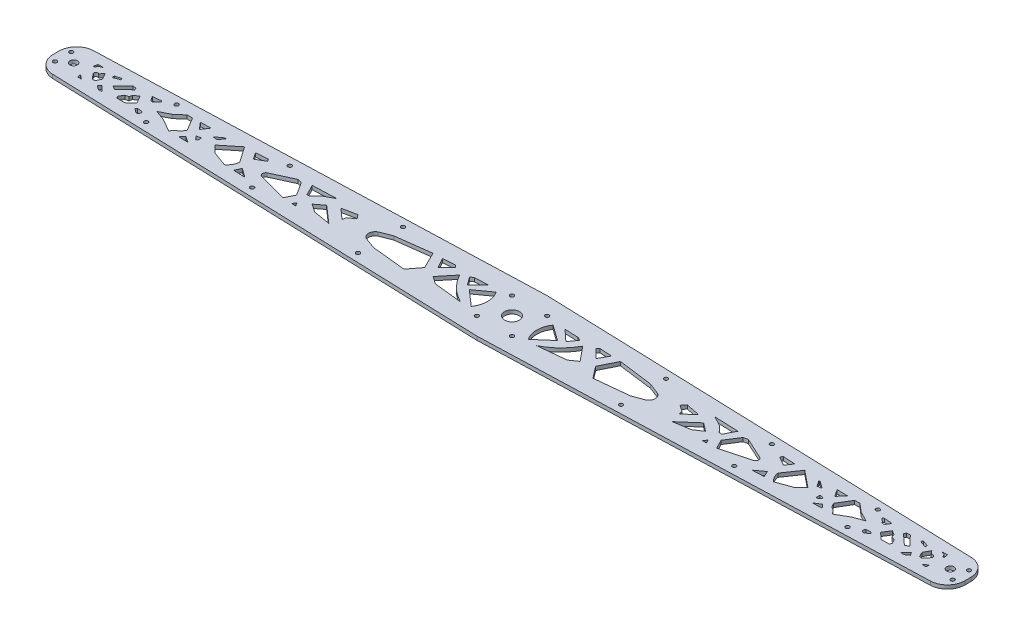
SolidWorks part; units mm, degrees
material "6061-T6 (SS)"
ref_plane "Front Plane" through (0, 0, 0) normal (0, 0, 1) x (1, 0, 0)
ref_plane "Top Plane" through (0, 0, 0) normal (0, 1, 0) x (1, 0, 0)
ref_plane "Right Plane" through (0, 0, 0) normal (1, 0, 0) x (0, 0, -1)
sketch "Sketch2" plane through (0, 0, 0) normal (0, 1, 0) x (1, 0, 0)
  line L0 (0, 0) -> (0, 30) construction
  line L1 (0, 0) -> (0, -30) construction
  line L2 (0, 0) -> (-375, 0) construction
  line L3 (-375, 17.5) -> (0, 30)
  line L4 (-375, -17.5) -> (0, -30)
  line L5 (375, -17.5) -> (0, -30)
  line L6 (375, 17.5) -> (0, 30)
  line L7 (-375, 17.5) -> (-375.4997, 17.4833)
  line L8 (-390, 2.4917) -> (-390, -2.4917)
  line L9 (-375.4997, -17.4833) -> (-375, -17.5)
  line L10 (-375, 17.5) -> (-375, -17.5) construction
  line L11 (390, 2.4917) -> (390, -2.4917)
  line L12 (375.4997, -17.4833) -> (375, -17.5)
  line L13 (375, 17.5) -> (375, -17.5) construction
  line L14 (375, 17.5) -> (375.4997, 17.4833)
  arc A2 (390, -2.4917) -> (375.4997, -17.4833) centre (375, -2.4917) cw
  arc A3 (390, 2.4917) -> (375.4997, 17.4833) centre (375, 2.4917) ccw
  arc A4 (-390, -2.4917) -> (-375.4997, -17.4833) centre (-375, -2.4917) ccw
  arc A5 (-375.4997, 17.4833) -> (-390, 2.4917) centre (-375, 2.4917) ccw
  point P15 (390, -17)
  point P18 (390, 17)
  point P21 (-390, -17)
  point P24 (-390, 17)
  point P26 (-390, 0)
  point P27 (390, 0)
  point P28 (375, 0)
  dimension "D4" = 15
  dimension "D1" = 60
  dimension "Half of Chassis Width" = 375
  dimension "FullLength" = 390
  dimension "D2" = 35
extrude "Boss-Extrude1" add sketch "Sketch2" along normal blind 3.18
sketch "Sketch3" plane through (0, 3.18, 0) normal (0, 1, 0) x (1, 0, 0)
  line L0 (0, 30) -> (0, -30) construction
  line L1 (-375, 0) -> (0, 0) construction
  line L2 (-390, 0) -> (-375, 0) construction
  line L3 (-206.25, 16.125) -> (-206.25, 0) construction
  line L4 (-112.5, -19.25) -> (-112.5, 0) construction
  line L5 (-390, 2.4917) -> (-390, -2.4917) construction
  line L6 (-375.4997, -17.4833) -> (0, -30) construction
  line L7 (-206.25, 16.125) -> (-206.25, 23.125) construction
  line L8 (0, 30) -> (-375.4997, 17.4833) construction
  line L9 (-112.5, -19.25) -> (-112.5, -26.25) construction
  line L10 (-375, 0) -> (-375, 17.5) construction
  line L11 (0, 30) -> (-375.4997, 17.4833) construction
  line L12 (-15, 0) -> (-15, 29.5) construction
  line L13 (-15, 15) -> (0, 15) construction
  line L14 (-300, 13) -> (-300, 0) construction
  line L15 (-300, 13) -> (-300, 20) construction
  circle A0 centre (0, 0) radius 6.35
  circle A1 centre (-375, 0) radius 3.175
  circle A3 centre (-206.25, 16.125) radius 1.65
  circle A4 centre (-112.5, -19.25) radius 1.65
  circle A8 centre (375, 0) radius 3.175
  circle A9 centre (-112.5, 19.25) radius 1.65
  circle A10 centre (-206.25, -16.125) radius 1.65
  circle A11 centre (112.5, -19.25) radius 1.65
  circle A12 centre (112.5, 19.25) radius 1.65
  circle A13 centre (206.25, -16.125) radius 1.65
  circle A14 centre (206.25, 16.125) radius 1.65
  circle A15 centre (-384, 7) radius 1.65
  circle A16 centre (-384, -7) radius 1.65
  circle A17 centre (384, -7) radius 1.65
  circle A18 centre (384, 7) radius 1.65
  circle A19 centre (-15, 15) radius 1.65
  circle A20 centre (-15, -15) radius 1.65
  circle A21 centre (15, -15) radius 1.65
  circle A22 centre (15, 15) radius 1.65
  circle A23 centre (-300, 13) radius 1.65
  circle A25 centre (-300, -13) radius 1.65
  circle A26 centre (300, -13) radius 1.65
  circle A27 centre (300, 13) radius 1.65
  dimension "D1" = 12.7
  dimension "D2" = 6.35
  dimension "D3" = 3.3
  dimension "Hole2" = 206.25
  dimension "Hole1" = 112.5
  dimension "D5" = 7
  dimension "D6" = 7
  dimension "BallJointHoles" = 375
  dimension "D4" = 9
  dimension "D7" = 7
  dimension "D8" = 15
  dimension "D9" = 15
  dimension "D10" = 7
  dimension "Hole3" = 300
extrude "Cut-Extrude1" cut sketch "Sketch3" against normal through all
sketch "Sketch7" plane through (0, 3.18, 0) normal (0, 1, 0) x (1, 0, 0)
  line L0 (-24.4071, -10.4422) -> (-37.738, 1.1764)
  line L1 (-37.738, 1.1764) -> (-24.4071, 10.7567)
  line L2 (-47.0329, 10.7567) -> (-42.1001, 3.9894)
  line L3 (-42.1001, 3.9894) -> (-32.5606, 12.795)
  line L5 (-62.9011, -4.6207) -> (-52.6865, 7.8247)
  line L6 (-32.5606, -11.6065) -> (-56.4435, -9.0822)
  line L7 (-56.4435, -9.0822) -> (-62.9011, -4.6207)
  line L8 (-67.5882, 4.294) -> (-60.2096, 11.6727)
  line L9 (-60.2096, 11.6727) -> (-61.9766, 13.4397)
  line L10 (-61.9766, 13.4397) -> (-72.2685, 12.795)
  line L11 (-72.2685, 12.795) -> (-67.5882, 4.294)
  line L12 (-47.0329, 10.7567) -> (-44.3117, 12.2755)
  line L13 (-44.3117, 12.2755) -> (-32.5606, 12.795)
  line L14 (-80.1851, 12.5584) -> (-73.1499, -1.5885)
  line L15 (-73.1499, -1.5885) -> (-80.8351, -11.6065)
  line L16 (-80.8351, -11.6065) -> (-109.8171, -8.6237)
  line L17 (-109.8171, -8.6237) -> (-119.4522, -5.1061)
  line L18 (-80.1851, 12.5584) -> (-109.8171, 8.7349)
  line L19 (-109.8171, 8.7349) -> (-119.4522, 4.9496)
  line L20 (-152.9555, 6.5926) -> (-140.8601, 9.0803)
  line L21 (-140.8601, 9.0803) -> (-138.158, 5.6061)
  line L22 (-138.158, 5.6061) -> (-143.5194, 1.9603)
  line L23 (-143.5194, 1.9603) -> (-144.1313, -1.2523)
  line L24 (-144.1313, -1.2523) -> (-152.9555, 6.5926)
  line L25 (-161.2336, 2.6701) -> (-146.9078, -9.8349)
  line L26 (-146.9078, -9.8349) -> (-161.2336, -7.5187)
  line L27 (-161.2336, -7.5187) -> (-168.3536, -2.7149)
  line L28 (-168.3536, -2.7149) -> (-161.2336, 2.6701)
  line L29 (-177.4895, -11.0358) -> (-174.0153, -11.0358)
  line L30 (-174.0153, -11.0358) -> (-175.7524, -8.1621)
  line L31 (-175.7524, -8.1621) -> (-177.4895, -11.0358)
  line L32 (-161.7297, 11.9502) -> (-182.144, 11.1941)
  line L33 (-182.144, 11.1941) -> (-177.4895, 2.1211)
  line L34 (-177.4895, 2.1211) -> (-175.1124, 2.1211)
  line L35 (-175.1124, 2.1211) -> (-170.3995, 7.2877)
  line L36 (-170.3995, 7.2877) -> (-161.7297, 11.9502)
  line L37 (-185.5062, -10.4422) -> (-181.6336, -2.7149)
  line L38 (-181.6336, -2.7149) -> (-188.9486, 8.7349)
  line L39 (-188.9486, 8.7349) -> (-192.6595, 9.5525)
  line L40 (-192.6595, 9.5525) -> (-210.8078, 1.1764)
  line L41 (-185.5062, -10.4422) -> (-210.0763, -3.869)
  line L45 (-224.6603, -6.0416) -> (-216.9788, -11.6065)
  line L46 (-216.9788, -11.6065) -> (-226.8789, -11.1945)
  line L47 (-226.8789, -11.1945) -> (-224.6603, -6.0416)
  line L48 (-230.6562, 11.1941) -> (-226.7322, 5.473)
  line L49 (-226.7322, 5.473) -> (-219.0389, 9.9382)
  line L50 (-219.0389, 9.9382) -> (-220.3165, 11.8009)
  line L51 (-220.3165, 11.8009) -> (-230.6562, 11.1941)
  line L52 (-234.9681, -11.0358) -> (-247.8251, -6.3663)
  line L53 (-247.8251, -6.3663) -> (-253.5886, -0.4545)
  line L54 (-253.5886, -0.4545) -> (-239.6062, 10.8696)
  line L55 (-239.6062, 10.8696) -> (-230.2889, -2.7149)
  line L56 (-260.5575, 4.815) -> (-254.4935, 9.2095)
  line L57 (-254.4935, 9.2095) -> (-253.4344, 9.0404)
  line L58 (-253.4344, 9.0404) -> (-256.7195, 4.294)
  line L59 (-256.7195, 4.294) -> (-260.5575, 4.815)
  line L60 (-264.6197, -4.507) -> (-264.6197, -1.0503)
  line L61 (-264.6197, -1.0503) -> (-268.3737, -1.8495)
  line L62 (-268.3737, -1.8495) -> (-266.1436, -4.507)
  line L63 (-266.1436, -4.507) -> (-264.6197, -4.507)
  line L64 (-267.017, -10.0823) -> (-272.4436, -6.6628)
  line L65 (-272.4436, -6.6628) -> (-275.1911, -9.8349)
  line L66 (-275.1911, -9.8349) -> (-267.017, -10.0823)
  line L67 (-271.8502, 4.294) -> (-276.7725, 10.1599)
  line L68 (-276.7725, 10.1599) -> (-267.8776, 10.3194)
  line L69 (-267.8776, 10.3194) -> (-271.8502, 4.294)
  line L70 (-283.2595, 9.9382) -> (-287.7962, 9.9382)
  line L71 (-287.7962, 9.9382) -> (-294.697, 3.9894)
  line L72 (-294.697, 3.9894) -> (-303.4188, -0.4545)
  line L73 (-303.4188, -0.4545) -> (-294.2177, -3.869)
  line L74 (-294.2177, -3.869) -> (-283.9624, -9.8349)
  line L75 (-283.9624, -9.8349) -> (-281.1829, -6.3663)
  line L76 (-281.1829, -6.3663) -> (-278.659, -5.1061)
  line L77 (-278.659, -5.1061) -> (-276.4865, -1.3434)
  line L78 (-276.4865, -1.3434) -> (-283.2595, 9.9382)
  line L79 (-311.5629, -10.2184) -> (-314.9575, -7.729)
  line L80 (-314.9575, -7.729) -> (-313.7334, -6.5049)
  line L81 (-313.7334, -6.5049) -> (-309.6085, -6.9575)
  line L82 (-314.7442, 6.0973) -> (-316.437, 8.7349)
  line L83 (-316.437, 8.7349) -> (-309.4364, 9.3537)
  line L84 (-309.4364, 9.3537) -> (-308.0306, 8.493)
  line L85 (-308.0306, 8.493) -> (-310.9283, 5.9682)
  line L86 (-330.2786, -7.729) -> (-323.5455, -7.729)
  line L87 (-323.5455, -7.729) -> (-318.0469, -2.7149)
  line L88 (-318.0469, -2.7149) -> (-321.8997, 3.5338)
  line L89 (-321.8997, 3.5338) -> (-325.723, 1.1764)
  line L90 (-325.723, 1.1764) -> (-326.3206, -1.3434)
  line L91 (-326.3206, -1.3434) -> (-329.119, -2.1893)
  line L92 (-329.119, -2.1893) -> (-331.4007, -6.0416)
  line L93 (-331.4007, -6.0416) -> (-330.2786, -7.729)
  line L94 (-340.8337, -0.4545) -> (-337.9048, -2.1893)
  line L95 (-337.9048, -2.1893) -> (-328.8174, 6.0973)
  line L96 (-328.8174, 6.0973) -> (-329.6427, 7.8247)
  line L97 (-329.6427, 7.8247) -> (-332.6351, 8.1721)
  line L98 (-332.6351, 8.1721) -> (-340.8337, -0.4545)
  line L99 (-347.4571, 5.6061) -> (-342.2812, 7.5649)
  line L100 (-347.6924, 7.5649) -> (-343.0084, 9.0404)
  line L101 (-341.7273, -9.0822) -> (-346.3347, -4.6207)
  line L102 (-346.3347, -4.6207) -> (-347.8648, -6.9575)
  line L103 (-347.8648, -6.9575) -> (-344.5811, -9.2944)
  line L104 (-344.5811, -9.2944) -> (-341.7273, -9.0822)
  line L105 (-362.8322, -8.8349) -> (-363.3101, -5.7891)
  line L106 (-363.3101, -5.7891) -> (-359.62, -8.8349)
  line L107 (-359.62, -8.8349) -> (-362.8322, -8.8349)
  line L108 (-358.5084, 9.2095) -> (-361.6705, 7.9391)
  line L109 (-361.6705, 7.9391) -> (-362.8322, 5.8039)
  line L110 (-362.8322, 5.8039) -> (-364.0328, 5.8039)
  line L111 (-364.0328, 5.8039) -> (-363.3101, 9.2095)
  line L112 (-363.3101, 9.2095) -> (-358.5084, 9.2095)
  line L113 (-353.551, 5.6061) -> (-350.6318, 0.1572)
  line L114 (-350.6318, 0.1572) -> (-352.4791, -3.6729)
  line L115 (-353.551, 5.6061) -> (-356.1053, 2.4847)
  line L116 (-355.5352, -3.4677) -> (-358.2947, -0.0783)
  line L117 (0, 30) -> (0, -30) construction
  line L118 (239.6062, 10.8696) -> (230.2889, -2.7149)
  line L119 (253.5886, -0.4545) -> (239.6062, 10.8696)
  line L120 (247.8251, -6.3663) -> (253.5886, -0.4545)
  line L121 (234.9681, -11.0358) -> (247.8251, -6.3663)
  line L122 (47.0329, 10.7567) -> (44.3117, 12.2755)
  line L123 (47.0329, 10.7567) -> (42.1001, 3.9894)
  line L124 (42.1001, 3.9894) -> (32.5606, 12.795)
  line L125 (44.3117, 12.2755) -> (32.5606, 12.795)
  line L126 (37.738, 1.1764) -> (24.4071, 10.7567)
  line L127 (24.4071, -10.4422) -> (37.738, 1.1764)
  line L128 (32.5606, -11.6065) -> (56.4435, -9.0822)
  line L129 (62.9011, -4.6207) -> (52.6865, 7.8247)
  line L130 (56.4435, -9.0822) -> (62.9011, -4.6207)
  line L131 (61.9766, 13.4397) -> (72.2685, 12.795)
  line L132 (60.2096, 11.6727) -> (61.9766, 13.4397)
  line L133 (67.5882, 4.294) -> (60.2096, 11.6727)
  line L134 (72.2685, 12.795) -> (67.5882, 4.294)
  line L135 (109.8171, 8.7349) -> (119.4522, 4.9496)
  line L136 (80.1851, 12.5584) -> (109.8171, 8.7349)
  line L137 (80.1851, 12.5584) -> (73.1499, -1.5885)
  line L138 (73.1499, -1.5885) -> (80.8351, -11.6065)
  line L139 (80.8351, -11.6065) -> (109.8171, -8.6237)
  line L140 (109.8171, -8.6237) -> (119.4522, -5.1061)
  line L141 (143.5194, 1.9603) -> (144.1313, -1.2523)
  line L142 (138.158, 5.6061) -> (143.5194, 1.9603)
  line L143 (140.8601, 9.0803) -> (138.158, 5.6061)
  line L144 (152.9555, 6.5926) -> (140.8601, 9.0803)
  line L145 (144.1313, -1.2523) -> (152.9555, 6.5926)
  line L146 (175.1124, 2.1211) -> (170.3995, 7.2877)
  line L147 (177.4895, 2.1211) -> (175.1124, 2.1211)
  line L148 (182.144, 11.1941) -> (177.4895, 2.1211)
  line L149 (161.7297, 11.9502) -> (182.144, 11.1941)
  line L150 (170.3995, 7.2877) -> (161.7297, 11.9502)
  line L151 (161.2336, -7.5187) -> (168.3536, -2.7149)
  line L152 (146.9078, -9.8349) -> (161.2336, -7.5187)
  line L153 (161.2336, 2.6701) -> (146.9078, -9.8349)
  line L154 (168.3536, -2.7149) -> (161.2336, 2.6701)
  line L155 (174.0153, -11.0358) -> (175.7524, -8.1621)
  line L156 (177.4895, -11.0358) -> (174.0153, -11.0358)
  line L157 (175.7524, -8.1621) -> (177.4895, -11.0358)
  line L158 (192.6595, 9.5525) -> (210.8078, 1.1764)
  line L159 (188.9486, 8.7349) -> (192.6595, 9.5525)
  line L160 (181.6336, -2.7149) -> (188.9486, 8.7349)
  line L161 (185.5062, -10.4422) -> (181.6336, -2.7149)
  line L162 (185.5062, -10.4422) -> (210.0763, -3.869)
  line L163 (219.0389, 9.9382) -> (220.3165, 11.8009)
  line L164 (226.7322, 5.473) -> (219.0389, 9.9382)
  line L165 (230.6562, 11.1941) -> (226.7322, 5.473)
  line L166 (220.3165, 11.8009) -> (230.6562, 11.1941)
  line L167 (216.9788, -11.6065) -> (226.8789, -11.1945)
  line L168 (224.6603, -6.0416) -> (216.9788, -11.6065)
  line L169 (226.8789, -11.1945) -> (224.6603, -6.0416)
  line L170 (276.7725, 10.1599) -> (267.8776, 10.3194)
  line L171 (271.8502, 4.294) -> (276.7725, 10.1599)
  line L172 (267.8776, 10.3194) -> (271.8502, 4.294)
  line L173 (253.4344, 9.0404) -> (256.7195, 4.294)
  line L174 (254.4935, 9.2095) -> (253.4344, 9.0404)
  line L175 (260.5575, 4.815) -> (254.4935, 9.2095)
  line L176 (256.7195, 4.294) -> (260.5575, 4.815)
  line L177 (268.3737, -1.8495) -> (266.1436, -4.507)
  line L178 (264.6197, -1.0503) -> (268.3737, -1.8495)
  line L179 (264.6197, -4.507) -> (264.6197, -1.0503)
  line L180 (266.1436, -4.507) -> (264.6197, -4.507)
  line L181 (272.4436, -6.6628) -> (275.1911, -9.8349)
  line L182 (267.017, -10.0823) -> (272.4436, -6.6628)
  line L183 (275.1911, -9.8349) -> (267.017, -10.0823)
  line L184 (278.659, -5.1061) -> (276.4865, -1.3434)
  line L185 (281.1829, -6.3663) -> (278.659, -5.1061)
  line L186 (283.9624, -9.8349) -> (281.1829, -6.3663)
  line L187 (294.2177, -3.869) -> (283.9624, -9.8349)
  line L188 (303.4188, -0.4545) -> (294.2177, -3.869)
  line L189 (294.697, 3.9894) -> (303.4188, -0.4545)
  line L190 (287.7962, 9.9382) -> (294.697, 3.9894)
  line L191 (283.2595, 9.9382) -> (287.7962, 9.9382)
  line L192 (276.4865, -1.3434) -> (283.2595, 9.9382)
  line L193 (313.7334, -6.5049) -> (309.6085, -6.9575)
  line L194 (314.9575, -7.729) -> (313.7334, -6.5049)
  line L195 (311.5629, -10.2184) -> (314.9575, -7.729)
  line L196 (314.7442, 6.0973) -> (316.437, 8.7349)
  line L197 (316.437, 8.7349) -> (309.4364, 9.3537)
  line L198 (309.4364, 9.3537) -> (308.0306, 8.493)
  line L199 (308.0306, 8.493) -> (310.9283, 5.9682)
  line L200 (329.119, -2.1893) -> (331.4007, -6.0416)
  line L201 (326.3206, -1.3434) -> (329.119, -2.1893)
  line L202 (325.723, 1.1764) -> (326.3206, -1.3434)
  line L203 (321.8997, 3.5338) -> (325.723, 1.1764)
  line L204 (318.0469, -2.7149) -> (321.8997, 3.5338)
  line L205 (323.5455, -7.729) -> (318.0469, -2.7149)
  line L206 (330.2786, -7.729) -> (323.5455, -7.729)
  line L207 (331.4007, -6.0416) -> (330.2786, -7.729)
  line L208 (329.6427, 7.8247) -> (332.6351, 8.1721)
  line L209 (328.8174, 6.0973) -> (329.6427, 7.8247)
  line L210 (337.9048, -2.1893) -> (328.8174, 6.0973)
  line L211 (340.8337, -0.4545) -> (337.9048, -2.1893)
  line L212 (332.6351, 8.1721) -> (340.8337, -0.4545)
  line L213 (347.4571, 5.6061) -> (342.2812, 7.5649)
  line L214 (347.6924, 7.5649) -> (343.0084, 9.0404)
  line L215 (347.8648, -6.9575) -> (344.5811, -9.2944)
  line L216 (346.3347, -4.6207) -> (347.8648, -6.9575)
  line L217 (341.7273, -9.0822) -> (346.3347, -4.6207)
  line L218 (344.5811, -9.2944) -> (341.7273, -9.0822)
  line L219 (363.3101, -5.7891) -> (359.62, -8.8349)
  line L220 (362.8322, -8.8349) -> (363.3101, -5.7891)
  line L221 (359.62, -8.8349) -> (362.8322, -8.8349)
  line L222 (355.5352, -3.4677) -> (358.2947, -0.0783)
  line L223 (353.551, 5.6061) -> (356.1053, 2.4847)
  line L224 (353.551, 5.6061) -> (350.6318, 0.1572)
  line L225 (350.6318, 0.1572) -> (352.4791, -3.6729)
  line L226 (364.0328, 5.8039) -> (363.3101, 9.2095)
  line L227 (362.8322, 5.8039) -> (364.0328, 5.8039)
  line L228 (361.6705, 7.9391) -> (362.8322, 5.8039)
  line L229 (358.5084, 9.2095) -> (361.6705, 7.9391)
  line L230 (363.3101, 9.2095) -> (358.5084, 9.2095)
  arc A0 (-24.4071, 10.7567) -> (-24.4071, -10.4422) centre (-39.8203, 0.1572) cw
  arc A1 (-52.6865, 7.8247) -> (-32.5606, -11.6065) centre (-11.1209, 30.738) ccw
  arc A2 (-119.4522, 4.9496) -> (-119.4522, -5.1061) centre (-116.9606, -0.0783) ccw
  arc A3 (-210.8078, 1.1764) -> (-210.0763, -3.869) centre (-209.5164, -1.2121) ccw
  arc A4 (-230.2889, -2.7149) -> (-234.9681, -11.0358) centre (-242.4659, -1.3434) cw
  arc A5 (-309.6085, -6.9575) -> (-311.5629, -10.2184) centre (-311.0256, -8.3243) cw
  arc A6 (-314.7442, 6.0973) -> (-310.9283, 5.9682) centre (-312.8149, 6.6637) ccw
  arc A7 (-343.0084, 9.0404) -> (-342.2812, 7.5649) centre (-343.3826, 7.9391) cw
  arc A8 (-347.4571, 5.6061) -> (-347.6924, 7.5649) centre (-345.8047, 6.7981) cw
  arc A9 (-358.2947, -0.0783) -> (-356.1053, 2.4847) centre (-357.2, 1.2032) cw
  arc A10 (-355.5352, -3.4677) -> (-352.4791, -3.6729) centre (-353.9045, -2.0423) ccw
  arc A11 (230.2889, -2.7149) -> (234.9681, -11.0358) centre (242.4659, -1.3434) ccw
  arc A12 (24.4071, 10.7567) -> (24.4071, -10.4422) centre (39.8203, 0.1572) ccw
  arc A13 (52.6865, 7.8247) -> (32.5606, -11.6065) centre (11.1209, 30.738) cw
  arc A14 (119.4522, 4.9496) -> (119.4522, -5.1061) centre (116.9606, -0.0783) cw
  arc A15 (210.8078, 1.1764) -> (210.0763, -3.869) centre (209.5164, -1.2121) cw
  arc A16 (309.6085, -6.9575) -> (311.5629, -10.2184) centre (311.0256, -8.3243) ccw
  arc A17 (314.7442, 6.0973) -> (310.9283, 5.9682) centre (312.8149, 6.6637) cw
  arc A18 (343.0084, 9.0404) -> (342.2812, 7.5649) centre (343.3826, 7.9391) ccw
  arc A19 (347.4571, 5.6061) -> (347.6924, 7.5649) centre (345.8047, 6.7981) ccw
  arc A20 (358.2947, -0.0783) -> (356.1053, 2.4847) centre (357.2, 1.2032) ccw
  arc A21 (355.5352, -3.4677) -> (352.4791, -3.6729) centre (353.9045, -2.0423) cw
extrude "Cut-Extrude3" cut sketch "Sketch7" against normal through all
equation "\"Hole2@Sketch3\"= \"Chassis Width@Differential System Assy - Option 1.Assembly\" / 2 * 0.55"
equation "\"Hole1@Sketch3\" = \"Chassis Width@Differential System Assy - Option 1.Assembly\" / 2 * 0.3"
equation "\"Half of Chassis Width@Sketch2\"= \"Chassis Width@Differential System Assy - Option 1.Assembly\" / 2"
equation "\"FullLength@Sketch2\"= \"Chassis Width@Differential System Assy - Option 1.Assembly\" / 2 * 1.04"
equation "\"BallJointHoles@Sketch3\"= \"Chassis Width@Differential System Assy - Option 1.Assembly\" / 2"
equation "\"Hole3@Sketch3\"= \"Chassis Width@Differential System Assy - Option 1.Assembly\" / 2 * 0.8"
